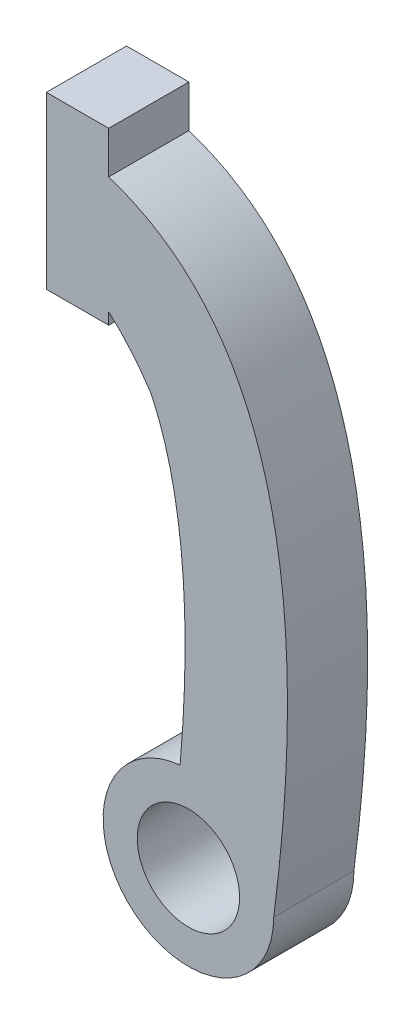
SolidWorks part; units mm, degrees
ref_plane "Front Plane" through (0, 0, 0) normal (0, 0, 1) x (1, 0, 0)
ref_plane "Top Plane" through (0, 0, 0) normal (0, 1, 0) x (1, 0, 0)
ref_plane "Right Plane" through (0, 0, 0) normal (1, 0, 0) x (0, 0, -1)
sketch "Sketch1" plane through (0, 0, 0) normal (0, 0, 1) x (1, 0, 0)
  line L0 (0, 0) -> (-130, 0) construction
  line L1 (-65, 0) -> (-65, 272.1192) construction
  line L3 (-22.0823, 230.1898) -> (-22.0823, 230.1898)
  line L4 (-46.7271, 258.9371) -> (-46.7271, 252.1192)
  line L5 (-83.2729, 352.1192) -> (-46.7271, 352.1192)
  line L6 (-83.2729, 352.1192) -> (-83.2729, 252.1192)
  line L7 (-83.2729, 252.1192) -> (-46.7271, 252.1192)
  line L8 (-46.7271, 352.1192) -> (-46.7271, 327.4313)
  line L9 (-83.2729, 352.1192) -> (-46.7271, 252.1192) construction
  line L10 (-83.2729, 252.1192) -> (-46.7271, 352.1192) construction
  line L12 (-65, 332.1192) -> (-65, 272.1192) construction
  circle A0 centre (0, 0) radius 30
  circle A1 centre (0, 0) radius 50
  circle A2 centre (-130, 0) radius 30
  circle A3 centre (-130, 0) radius 50
  spline S0 degree 2 poles (50, 0) (89.5388, 302.3866) (-65, 332.1192) knots 0 0 0 0.820923 0.820923 0.820923
  spline S1 degree 1 poles (-9.4936, 7.7791) (-22.0823, 230.1898) knots 0 0 1 1 construction
  spline S2 degree 3 poles (-9.4936, 7.7791) (-9.2715, 9.4777) (-8.8335, 12.8884) (-8.0018, 19.6142) (-7.0362, 27.9108) (-5.9982, 37.6671) (-4.7733, 50.4158) (-3.5396, 65.8581) (-2.5294, 83.5914) (-1.9823, 100.5167) (-1.8588, 121.9921) (-2.815, 146.7608) (-5.1569, 168.6796) (-7.7757, 184.4586) (-10.0839, 195.4064) (-12.7043, 205.4624) (-15.1177, 213.0998) (-17.166, 218.7682) (-18.7563, 222.8021) (-20.1205, 225.981) (-21.2365, 228.4246) (-21.7957, 229.5998) (-22.0823, 230.1898) knots 0 0 0 0 0.007323 0.014646 0.029292 0.043938 0.058584 0.087876 0.117168 0.14646 0.175752 0.234336 0.292921 0.322213 0.351505 0.380797 0.410089 0.424735 0.439381 0.454027 0.46135 0.468673 0.468673 0.468673 0.468673 only from (-4.87, 49.7623) to (-22.0823, 230.1898)
  spline S3 degree 2 poles (-22.0823, 230.1898) (-40.6909, 258.1491) (-65, 272.1192) knots 0 0 0 0.333582 0.333582 0.333582
  point P16 (-65, 302.1192)
  dimension "D1" = 60
  dimension "D3" = 130
  dimension "D5" = 60
  dimension "D6" = 60
  dimension "D7" = 20
  dimension "D2" = 20
  dimension "D4" = 20
extrude "Boss-Extrude1" add sketch "Sketch1" along normal blind 47
